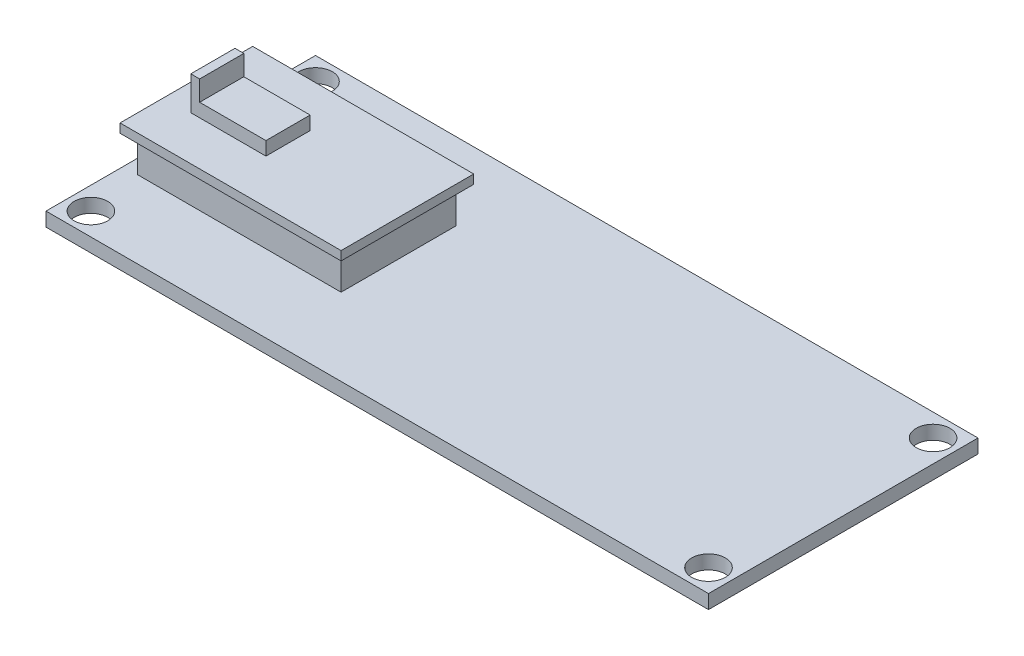
SolidWorks part; units mm, degrees
ref_plane "Front Plane" through (0, 0, 0) normal (0, 0, 1) x (1, 0, 0)
ref_plane "Top Plane" through (0, 0, 0) normal (0, 1, 0) x (1, 0, 0)
ref_plane "Right Plane" through (0, 0, 0) normal (1, 0, 0) x (0, 0, -1)
sketch "Sketch1" plane through (0, 0, 0) normal (0, 1, 0) x (1, 0, 0)
  line L5 (-37.465, -15.24) -> (37.465, -15.24)
  line L6 (-37.465, -15.24) -> (-37.465, 15.24)
  line L7 (-37.465, 15.24) -> (37.465, 15.24)
  line L8 (37.465, -15.24) -> (37.465, 15.24)
  line L9 (-37.465, -15.24) -> (37.465, 15.24) construction
  line L10 (-37.465, 15.24) -> (37.465, -15.24) construction
  line L15 (-34.925, -12.7) -> (34.925, -12.7) construction
  line L16 (-34.925, -12.7) -> (-34.925, 12.7) construction
  line L17 (-34.925, 12.7) -> (34.925, 12.7) construction
  line L18 (34.925, -12.7) -> (34.925, 12.7) construction
  line L19 (-34.925, -12.7) -> (34.925, 12.7) construction
  line L20 (-34.925, 12.7) -> (34.925, -12.7) construction
  circle A0 centre (-34.925, 12.7) radius 1.905
  circle A1 centre (34.925, 12.7) radius 1.905
  circle A2 centre (-34.925, -12.7) radius 1.905
  circle A3 centre (34.925, -12.7) radius 1.905
  point P0 (0, 0)
  point P5 (0, 0)
extrude "Boss-Extrude1" add sketch "Sketch1" against normal blind 1.5748
sketch "Sketch2" plane through (0, 0, 0) normal (0, 1, 0) x (1, 0, 0)
  line L0 (-37.465, 15.24) -> (-37.465, -15.24) construction
  line L1 (37.465, -15.24) -> (37.465, 15.24) construction
  line L2 (-1000, 0) -> (49000, 0) construction
  line L3 (-36.83, 12.7) -> (-36.83, -12.7) construction
  line L4 (-36.83, -7.5) -> (-36.83, 7.5) construction
  line L5 (-36.83, 0) -> (-11.83, 0)
  line L6 (-11.83, -7.5) -> (-11.83, 7.5) construction
  line L8 (-36.83, -7.5) -> (-11.83, -7.5)
  line L9 (-36.83, -7.5) -> (-36.83, 7.5)
  line L10 (-36.83, 7.5) -> (-11.83, 7.5)
  line L11 (-11.83, -7.5) -> (-11.83, 7.5)
  circle A0 centre (-34.925, 12.7) radius 1.905 construction
  circle A1 centre (-34.925, -12.7) radius 1.905 construction
  point P0 (-37.465, 0)
  point P1 (37.465, 0)
  point P7 (-36.83, 12.7)
  point P10 (-36.83, -12.7)
  point P20 (-36.83, 0)
  point P25 (-11.83, 0)
extrude "Boss-Extrude2" add sketch "Sketch2" along normal blind 5.08 contours L5 L11 L10 L9 | L8 L11 L5 L9
sketch "Sketch3" plane through (0, 5.08, 0) normal (0, 1, 0) x (1, 0, 0)
  line L0 (-36.83, -7.5) -> (-11.83, -7.5) construction
  line L1 (-36.83, -7.5) -> (-36.83, 7.5) construction
  line L3 (-35.83, 6.5) -> (-12.83, 6.5)
  line L4 (-35.83, 6.5) -> (-35.83, -6.5)
  line L5 (-35.83, -6.5) -> (-12.83, -6.5)
  line L6 (-12.83, 6.5) -> (-12.83, -6.5)
  line L7 (-36.83, 7.5) -> (-11.83, 7.5)
  line L8 (-36.83, 7.5) -> (-36.83, -7.5)
  line L9 (-36.83, -7.5) -> (-11.83, -7.5)
  line L10 (-11.83, 7.5) -> (-11.83, -7.5)
  point P0 (-36.83, 7.5)
  point P1 (-11.83, -7.5)
  point P3 (-11.83, 7.5)
  point P5 (-36.83, -7.5)
  point P7 (-35.83, -7.5)
  point P9 (-36.83, 6.5)
  point P12 (-36.83, -6.5)
  point P15 (-12.83, -7.5)
  point P16 (-35.83, -6.5)
  point P17 (-12.83, -6.5)
  point P18 (-35.83, 6.5)
  point P19 (-12.83, 6.5)
  dimension "D1" = 1
  dimension "D2" = 1
  dimension "D3" = 1
  dimension "D4" = 1
extrude "Cut-Extrude1" cut sketch "Sketch3" against normal blind 4.064 from offset 1.016 offset against normal yes
sketch "Sketch4" plane through (0, 5.08, 0) normal (0, 1, 0) x (1, 0, 0)
  line L0 (-36.83, -7.5) -> (-11.83, -7.5) construction
  line L1 (-11.83, -7.5) -> (-11.83, 7.5) construction
  line L2 (-36.83, -7.5) -> (-36.83, 7.5) construction
  line L3 (-36.83, -2.5) -> (-36.83, 2.5) construction
  line L5 (-33.83, -2.5) -> (-25.33, -2.5)
  line L6 (-33.83, -2.5) -> (-33.83, 2.5)
  line L7 (-33.83, 2.5) -> (-25.33, 2.5)
  line L8 (-25.33, -2.5) -> (-25.33, 2.5)
  point P0 (-36.83, -7.5)
  point P1 (-33.83, -7.5)
  point P3 (-11.83, -7.5)
  point P6 (-24.33, -7.5)
  point P9 (-25.33, -7.5)
  point P10 (-36.83, 0)
  point P16 (-36.83, 0)
  dimension "D1" = 3
  dimension "D2" = 1
extrude "Boss-Extrude3" add sketch "Sketch4" along normal blind 1.524 contours L6 L5 L8 L7
sketch "Sketch5" plane through (0, 6.604, 0) normal (0, 1, 0) x (1, 0, 0)
  line L0 (-33.83, -2.5) -> (-25.33, -2.5) construction
  line L2 (-32.83, -2.5) -> (-33.83, -2.5)
  line L3 (-32.83, -2.5) -> (-32.83, 2.5)
  line L4 (-32.83, 2.5) -> (-33.83, 2.5)
  line L5 (-33.83, -2.5) -> (-33.83, 2.5)
  point P0 (-33.83, -2.5)
  point P1 (-32.83, -2.5)
  dimension "D1" = 1
extrude "Boss-Extrude4" add sketch "Sketch5" along normal blind 2.286
